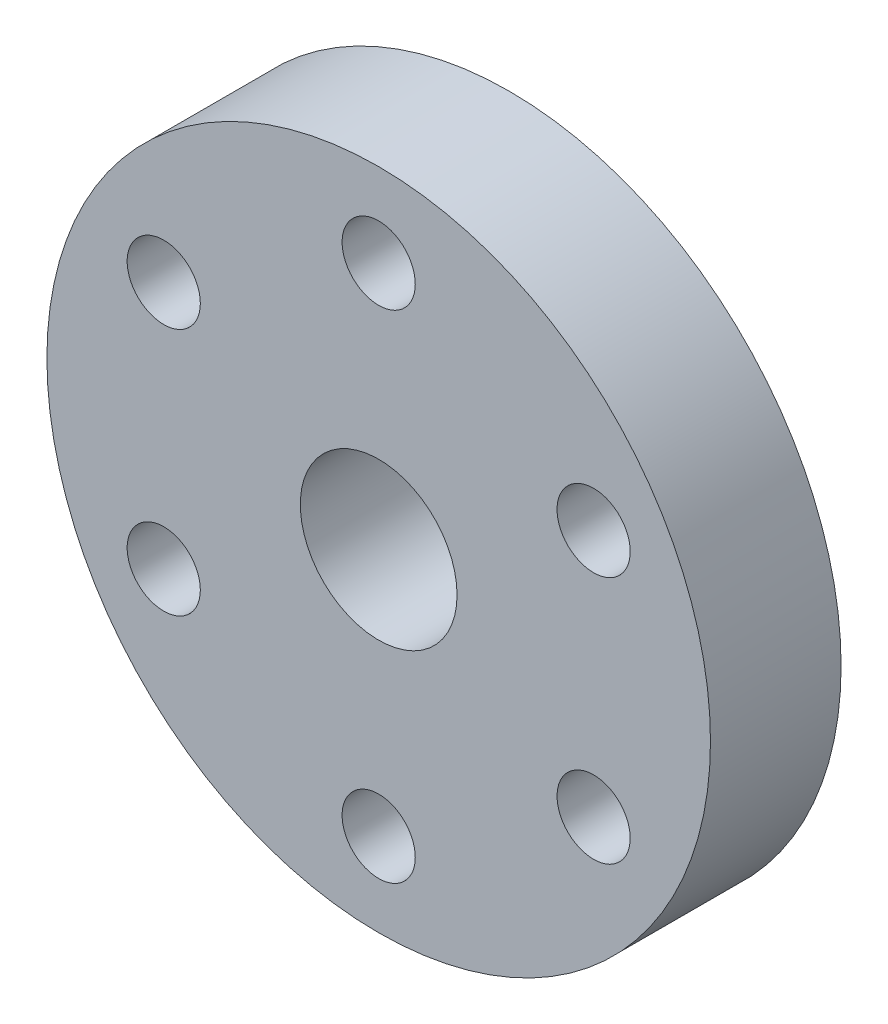
SolidWorks part; units mm, degrees
material "1060 Alloy"
ref_plane "Front Plane" through (0, 0, 0) normal (0, 0, 1) x (1, 0, 0)
ref_plane "Top Plane" through (0, 0, 0) normal (0, 1, 0) x (1, 0, 0)
ref_plane "Right Plane" through (0, 0, 0) normal (1, 0, 0) x (0, 0, -1)
sketch "Sketch1" plane through (0, 0, 0) normal (0, 0, 1) x (1, 0, 0)
  circle A0 centre (0, 0) radius 6
  circle A1 centre (0, 0) radius 3
  dimension "D1" = 12
  dimension "D2" = 6
extrude "Boss-Extrude1" add sketch "Sketch1" along normal blind 4.2
sketch "Sketch2" plane through (0, 0, 4.2) normal (0, 0, 1) x (1, 0, 0)
  circle A0 centre (0, 0) radius 12.7
  circle A1 centre (0, 0) radius 3
  dimension "D1" = 25.4
extrude "Boss-Extrude2" add sketch "Sketch2" along normal blind 5
sketch "Sketch3" plane through (0, 0, 0) normal (0, 1, 0) x (1, 0, 0)
  line L0 (0, 0) -> (0, -2.1) construction
  circle A0 centre (0, -2.1) radius 1.4
  dimension "D2" = 2.8
  dimension "D1" = 2.1
extrude "Cut-Extrude1" cut sketch "Sketch3" against normal through all
sketch "Sketch4" plane through (0, 0, 9.2) normal (0, 0, 1) x (1, 0, 0)
  circle A1 centre (0, 9.5) radius 1.4
  circle A2 centre (8.2272, 4.75) radius 1.4
  circle A3 centre (8.2272, -4.75) radius 1.4
  circle A4 centre (0, -9.5) radius 1.4
  circle A5 centre (-8.2272, -4.75) radius 1.4
  circle A6 centre (-8.2272, 4.75) radius 1.4
  point P18 (0, 0)
  dimension "D2" = 2.8
  dimension "D3" = 6
extrude "Cut-Extrude2" cut sketch "Sketch4" against normal blind 5
